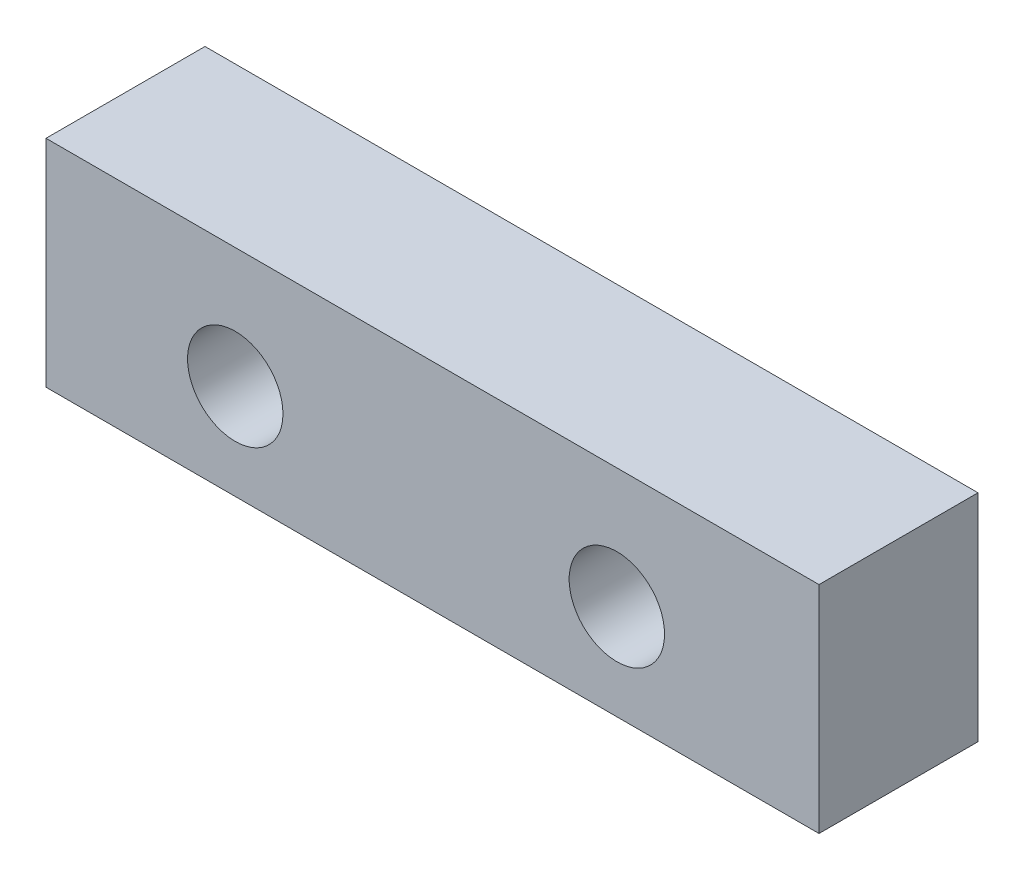
SolidWorks part; units mm, degrees
material "Acrylic (Medium-high impact)"
ref_plane "Front Plane" through (0, 0, 0) normal (0, 0, 1) x (1, 0, 0)
ref_plane "Top Plane" through (0, 0, 0) normal (0, 1, 0) x (1, 0, 0)
ref_plane "Right Plane" through (0, 0, 0) normal (1, 0, 0) x (0, 0, -1)
sketch "Sketch1" plane through (0, 0, 0) normal (0, 0, 1) x (1, 0, 0)
  line L1 (-7.6067, 2.067) -> (16.7017, 2.067)
  line L2 (-7.6067, 2.067) -> (-7.6067, -4.7129)
  line L3 (-7.6067, -4.7129) -> (16.7017, -4.7129)
  line L4 (16.7017, 2.067) -> (16.7017, -4.7129)
  circle A0 centre (-1.6553, -1.7129) radius 1.5
  circle A1 centre (10.3447, -1.7129) radius 1.5
extrude "Boss-Extrude1" add sketch "Sketch1" along normal blind 5
